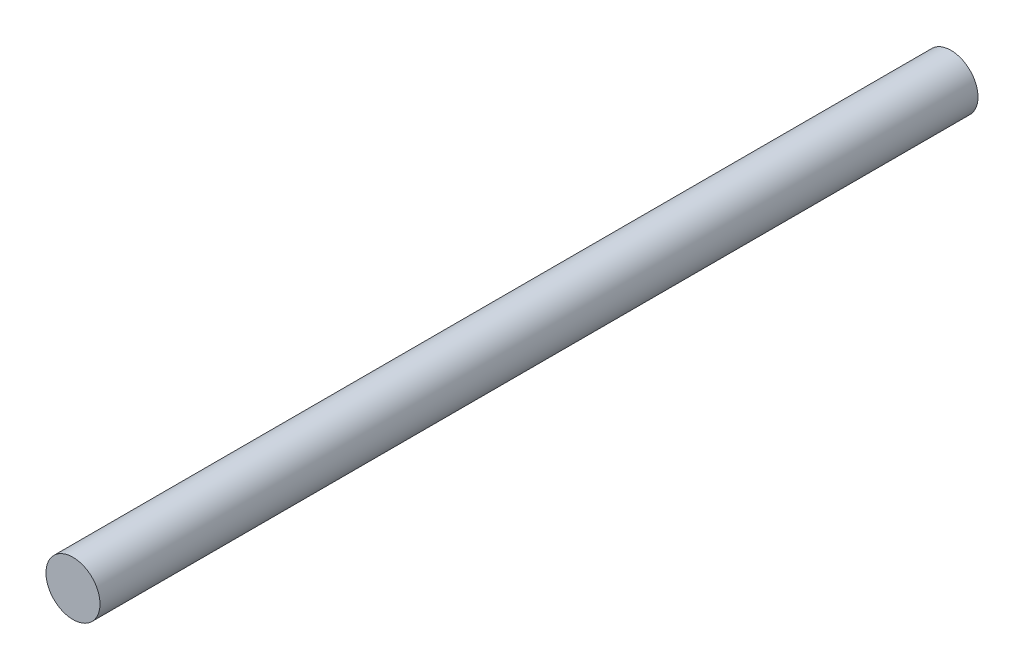
SolidWorks part; units mm, degrees
ref_plane "Front Plane" through (0, 0, 0) normal (0, 0, 1) x (1, 0, 0)
ref_plane "Top Plane" through (0, 0, 0) normal (0, 1, 0) x (1, 0, 0)
ref_plane "Right Plane" through (0, 0, 0) normal (1, 0, 0) x (0, 0, -1)
sketch "Sketch1" plane through (0, 0, 0) normal (0, 0, 1) x (1, 0, 0)
  circle A0 centre (0, 0) radius 4
  dimension "D1" = 8
extrude "Boss-Extrude1" add sketch "Sketch1" along normal blind 130
